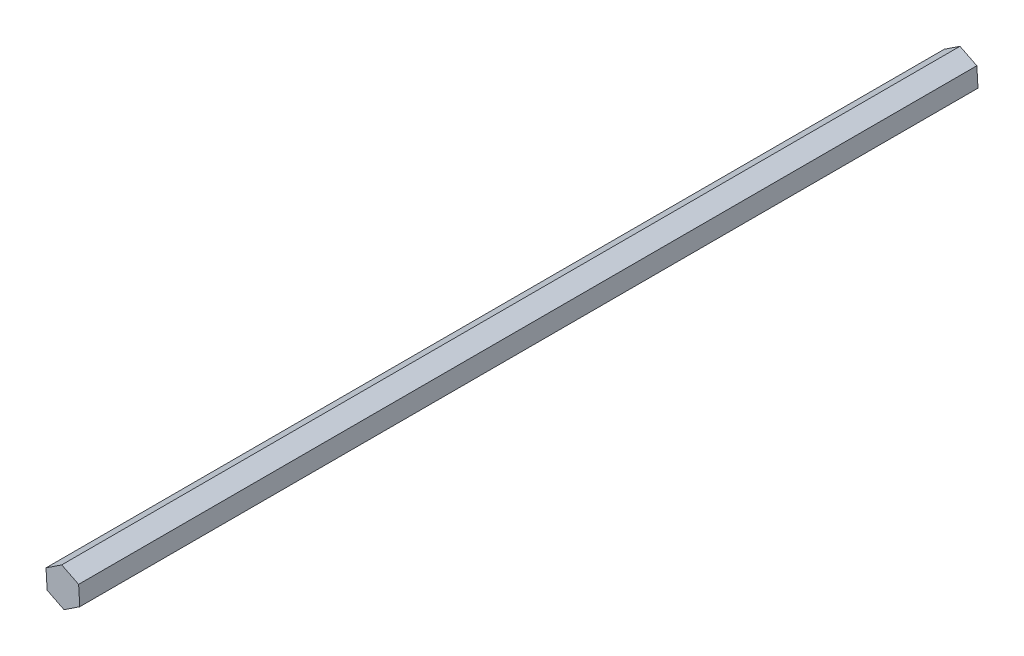
SolidWorks part; units mm, degrees
ref_plane "Front Plane" through (0, 0, 0) normal (0, 0, 1) x (1, 0, 0)
ref_plane "Top Plane" through (0, 0, 0) normal (0, 1, 0) x (1, 0, 0)
ref_plane "Right Plane" through (0, 0, 0) normal (1, 0, 0) x (0, 0, -1)
sketch "Sketch1" plane through (0, 0, 0) normal (0, 0, 1) x (1, 0, 0)
  line L1 (-0.4538, 7.336) -> (-6.58, 3.275)
  line L2 (-6.58, 3.275) -> (-6.1263, -4.061)
  line L3 (-6.1263, -4.061) -> (0.4538, -7.336)
  line L4 (0.4538, -7.336) -> (6.58, -3.275)
  line L5 (6.58, -3.275) -> (6.1263, 4.061)
  line L6 (6.1263, 4.061) -> (-0.4538, 7.336)
  circle A0 centre (0, 0) radius 6.3653 construction
  dimension "D1" = 7.35
extrude "Boss-Extrude1" add sketch "Sketch1" along normal blind 350
